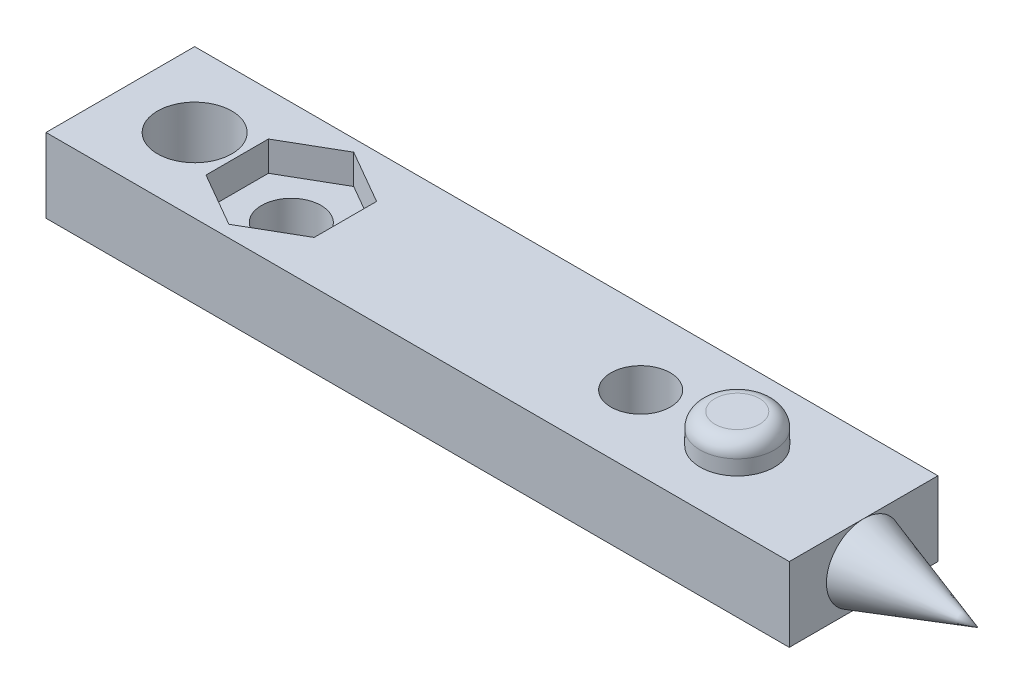
SolidWorks part; units mm, degrees
ref_plane "Front Plane" through (0, 0, 0) normal (0, 0, 1) x (1, 0, 0)
ref_plane "Top Plane" through (0, 0, 0) normal (0, 1, 0) x (1, 0, 0)
ref_plane "Right Plane" through (0, 0, 0) normal (1, 0, 0) x (0, 0, -1)
sketch "Sketch1" plane through (0, 0, 0) normal (0, 1, 0) x (1, 0, 0)
  line L1 (0, 0) -> (50, 0)
  line L2 (0, 0) -> (0, 10)
  line L3 (0, 10) -> (50, 10)
  line L4 (50, 0) -> (50, 10)
  dimension "D1" = 10
  dimension "D2" = 50
extrude "Boss-Extrude1" add sketch "Sketch1" along normal blind 5
sketch "Sketch2" plane through (0, 0, 0) normal (0, -1, 0) x (1, 0, 0)
  line L0 (0, -10) -> (0, 0) construction
  line L1 (0, 0) -> (50, 0) construction
  circle A0 centre (5, -5) radius 2.5
  circle A1 centre (11.5, -5) radius 2
  dimension "D1" = 4
  dimension "D2" = 5
  dimension "D3" = 6.5
  dimension "D4" = 5
  dimension "D5" = 5
extrude "Cut-Extrude1" cut sketch "Sketch2" against normal blind 5
sketch "Sketch3" plane through (0, 5, 0) normal (0, 1, 0) x (1, 0, 0)
  line L1 (50, 10) -> (0, 10) construction
  line L2 (0, 10) -> (0, 0) construction
  circle A0 centre (35, 5) radius 2
  dimension "D1" = 4
  dimension "D4" = 5
  dimension "D5" = 35
extrude "Cut-Extrude2" cut sketch "Sketch3" against normal blind 5
sketch "Sketch4" plane through (0, 5, 0) normal (0, 1, 0) x (1, 0, 0)
  line L1 (11.5, 0.8) -> (15.1373, 2.9)
  line L2 (15.1373, 2.9) -> (15.1373, 7.1)
  line L3 (15.1373, 7.1) -> (11.5, 9.2)
  line L4 (11.5, 9.2) -> (7.8627, 7.1)
  line L5 (7.8627, 7.1) -> (7.8627, 2.9)
  line L6 (7.8627, 2.9) -> (11.5, 0.8)
  circle A0 centre (11.5, 5) radius 4.2 construction
extrude "Cut-Extrude3" cut sketch "Sketch4" against normal blind 2
sketch "Sketch5" plane through (0, 5, 0) normal (0, 1, 0) x (1, 0, 0)
  line L0 (0, 0) -> (50, 0) construction
  circle A0 centre (41.5, 5) radius 2.5
  circle A1 centre (35, 5) radius 2 construction
  dimension "D1" = 5
  dimension "D2" = 6.5
  dimension "D3" = 5
extrude "Boss-Extrude2" add sketch "Sketch5" along normal blind 2
fillet "Fillet1" radius 1 1 edges at (41.5, 7, -2.5)
sketch "Sketch7" plane through (50, 0, 0) normal (1, 0, 0) x (0, 0, -1)
  line L0 (0, 5) -> (10, 5) construction
  line L1 (0, 5) -> (0, 0) construction
  circle A0 centre (5, 2.5) radius 2.5
  point P4 (5, 5)
  point P7 (0, 2.5)
  dimension "D1" = 5
extrude "Boss-Extrude3" add sketch "Sketch7" along normal blind 8 draft 18
